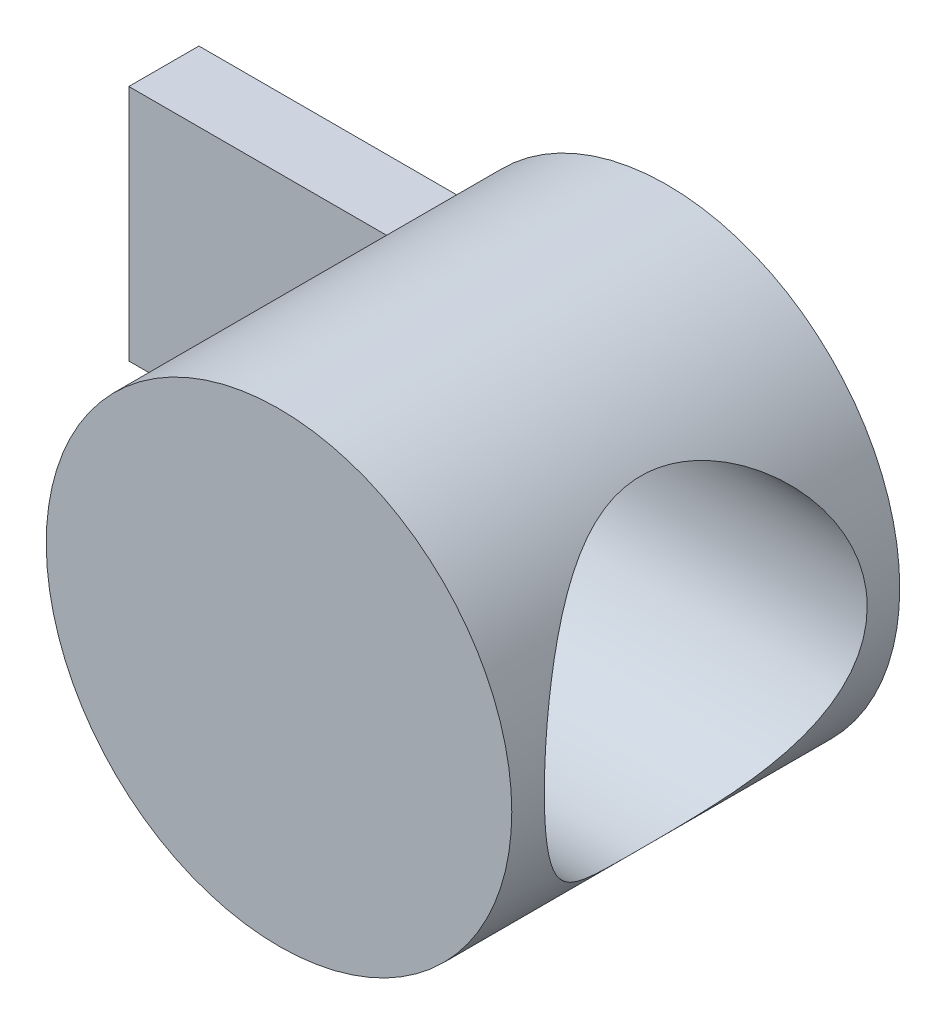
SolidWorks part; units mm, degrees
material "ЦА4М3 ГОСТ 25140-93"
ref_plane "Спереди" through (0, 0, 0) normal (0, 0, 1) x (1, 0, 0)
ref_plane "Сверху" through (0, 0, 0) normal (0, 1, 0) x (1, 0, 0)
ref_plane "Справа" through (0, 0, 0) normal (1, 0, 0) x (0, 0, -1)
sketch "Эскиз1" plane through (0, 0, 0) normal (0, 0, 1) x (1, 0, 0)
  circle A0 centre (0, 0) radius 9.3
  dimension "D1" = 9.3
extrude "Бобышка-Вытянуть1" add sketch "Эскиз1" along normal blind 15.5
sketch "Эскиз2" plane through (0, 0, 0) normal (0, 0, 1) x (1, 0, 0)
  line L1 (-7.9955, 4.75) -> (-18.7, 4.75)
  line L2 (-7.9955, 4.75) -> (-7.9955, -4.75)
  line L3 (-7.9955, -4.75) -> (-18.7, -4.75)
  line L4 (-18.7, 4.75) -> (-18.7, -4.75)
  circle A0 centre (0, 0) radius 9.3 construction
  dimension "D1" = 28
  dimension "D2" = 9.5
extrude "Бобышка-Вытянуть2" add sketch "Эскиз2" along normal blind 2.8
sketch "Эскиз3" plane through (0, 0, 0) normal (1, 0, 0) x (0, 0, -1)
  line L0 (-7.75, 9.3) -> (-7.75, 0) construction
  line L1 (0, 9.3) -> (-15.5, 9.3) construction
  circle A0 centre (-7.75, 0) radius 6.45
  dimension "D1" = 12.9
extrude "Вырез-Вытянуть1" cut sketch "Эскиз3" along normal through all and the other way blind 2
sketch "Эскиз4" plane through (-2, 0, 0) normal (1, 0, 0) x (0, 0, -1)
  circle A0 centre (-7.75, 0) radius 4
  dimension "D1" = 8
extrude "Вырез-Вытянуть2" cut sketch "Эскиз4" against normal through all
